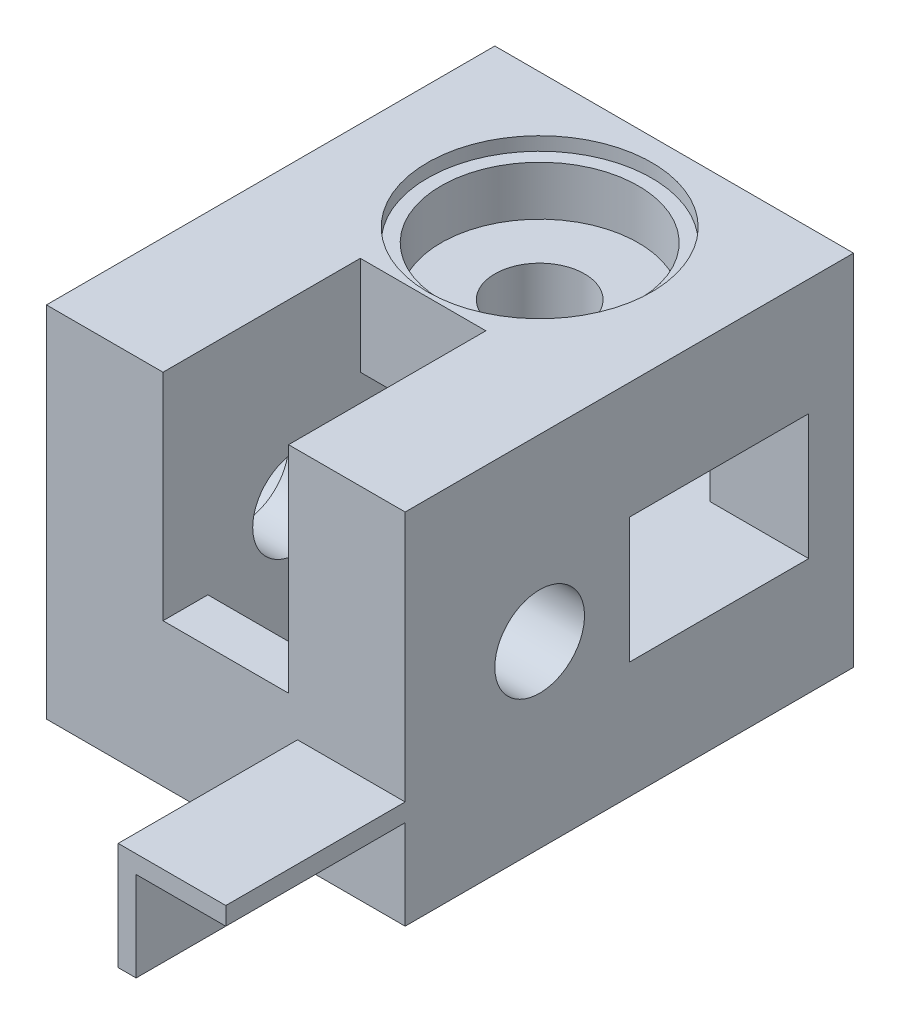
SolidWorks part; units mm, degrees
ref_plane "Plan de face" through (0, 0, 0) normal (0, 0, 1) x (1, 0, 0)
ref_plane "Plan de dessus" through (0, 0, 0) normal (0, 1, 0) x (1, 0, 0)
ref_plane "Plan de droite" through (0, 0, 0) normal (1, 0, 0) x (0, 0, -1)
sketch "Esquisse1" plane through (0, 0, 0) normal (0, 0, 1) x (1, 0, 0)
  line L1 (-40, 40) -> (0, 40)
  line L2 (-40, 40) -> (-40, 0)
  line L3 (-40, 0) -> (0, 0)
  line L4 (0, 40) -> (0, 0)
  dimension "D1" = 40
  dimension "D2" = 40
extrude "Boss.-Extru.1" add sketch "Esquisse1" along normal blind 50
sketch "Esquisse2" plane through (0, 40, 0) normal (0, 1, 0) x (1, 0, 0)
  line L0 (0, 0) -> (-40, 0) construction
  line L1 (-40, -50) -> (-40, 0) construction
  circle A0 centre (-20, -15) radius 5
  dimension "D1" = 10
  dimension "D2" = 15
  dimension "D3" = 20
extrude "Enlèv. mat.-Extru.1" cut sketch "Esquisse2" against normal through all
sketch "Esquisse3" plane through (-40, 0, 0) normal (-1, 0, 0) x (0, 0, 1)
  line L0 (50, 40) -> (50, 0) construction
  line L1 (50, 40) -> (0, 40) construction
  circle A0 centre (35, 20) radius 5
  dimension "D1" = 10
  dimension "D2" = 15
  dimension "D3" = 20
extrude "Enlèv. mat.-Extru.2" cut sketch "Esquisse3" against normal through all
sketch "Esquisse4" plane through (-40, 0, 0) normal (-1, 0, 0) x (0, 0, 1)
  line L1 (22, 27) -> (0, 27)
  line L2 (22, 27) -> (22, 13)
  line L3 (22, 13) -> (0, 13)
  line L4 (0, 27) -> (0, 13)
  line L5 (0, 40) -> (0, 0) construction
  line L6 (50, 0) -> (0, 0) construction
  line L7 (50, 40) -> (0, 40) construction
  dimension "D1" = 14
  dimension "D2" = 22
  dimension "D3" = 0
  dimension "D4" = 13
  dimension "D5" = 13
extrude "Enlèv. mat.-Extru.3" cut sketch "Esquisse4" against normal blind 29
sketch "Esquisse5" plane through (0, 0, 0) normal (0, -1, 0) x (1, 0, 0)
  line L0 (-40, 50) -> (0, 50) construction
  line L1 (-13, 25) -> (-27, 25)
  line L2 (-13, 25) -> (-13, 45)
  line L3 (-13, 45) -> (-27, 45)
  line L4 (-27, 25) -> (-27, 45)
  line L5 (-40, 50) -> (-40, 0) construction
  dimension "D1" = 20
  dimension "D2" = 5
  dimension "D3" = 14
  dimension "D4" = 13
extrude "Enlèv. mat.-Extru.4" cut sketch "Esquisse5" against normal blind 29
sketch "Esquisse6" plane through (0, 0, 0) normal (1, 0, 0) x (0, 0, -1)
  line L1 (-5, 27) -> (-25, 27)
  line L2 (0, 0) -> (0, 40) construction
  line L3 (-5, 13) -> (-25, 13)
  line L4 (-25, 27) -> (-25, 13)
  line L5 (-50, 0) -> (0, 0) construction
  line L6 (-5, 27) -> (-5, 13)
  dimension "D1" = 14
  dimension "D2" = 5
  dimension "D3" = 13
  dimension "D4" = 20
extrude "Enlèv. mat.-Extru.5" cut sketch "Esquisse6" against normal blind 24
sketch "Esquisse7" plane through (0, 40, 0) normal (0, 1, 0) x (1, 0, 0)
  line L0 (0, -50) -> (-40, -50) construction
  line L1 (-27, -50) -> (-13, -50)
  line L2 (-27, -50) -> (-27, -28)
  line L3 (-27, -28) -> (-13, -28)
  line L4 (-13, -50) -> (-13, -28)
  line L5 (-40, -50) -> (-40, 0) construction
  dimension "D1" = 14
  dimension "D2" = 22
  dimension "D3" = 13
extrude "Enlèv. mat.-Extru.6" cut sketch "Esquisse7" against normal blind 24
sketch "Esquisse10" plane through (0, 40, 0) normal (0, 1, 0) x (1, 0, 0)
  circle A0 centre (-20, -15) radius 11
  dimension "D1" = 22
extrude "Enlèv. mat.-Extru.9" cut sketch "Esquisse10" against normal blind 7
sketch "Esquisse11" plane through (0, 40, 0) normal (0, 1, 0) x (1, 0, 0)
  circle A0 centre (-20, -15) radius 12.5
  dimension "D1" = 25
extrude "Enlèv. mat.-Extru.10" cut sketch "Esquisse11" against normal blind 1.5
sketch "Esquisse13" plane through (0, 0, 50) normal (0, 0, 1) x (1, 0, 0)
  line L3 (-40, 0) -> (0, 0) construction
  line L8 (-10, 0) -> (-10, 10)
  line L9 (-10, 10) -> (0, 10)
  line L10 (0, 0) -> (0, 40) construction
  line L11 (0, 10) -> (0, 12)
  line L12 (0, 12) -> (-12, 12)
  line L13 (-12, 12) -> (-12, 0)
  line L14 (-12, 0) -> (-10, 0)
  dimension "D5" = 12
  dimension "D6" = 12
  dimension "D7" = 2
  dimension "D8" = 2
extrude "Boss.-Extru.2" add sketch "Esquisse13" along normal blind 20
sketch "Esquisse14" plane through (-40, 0, 0) normal (-1, 0, 0) x (0, 0, 1)
  circle A0 centre (35, 20) radius 11
  dimension "D1" = 22
extrude "Enlèv. mat.-Extru.11" cut sketch "Esquisse14" against normal blind 7
sketch "Esquisse15" plane through (-40, 0, 0) normal (-1, 0, 0) x (0, 0, 1)
  circle A0 centre (35, 20) radius 12.5
  dimension "D1" = 25
extrude "Enlèv. mat.-Extru.12" cut sketch "Esquisse15" against normal blind 1.5
